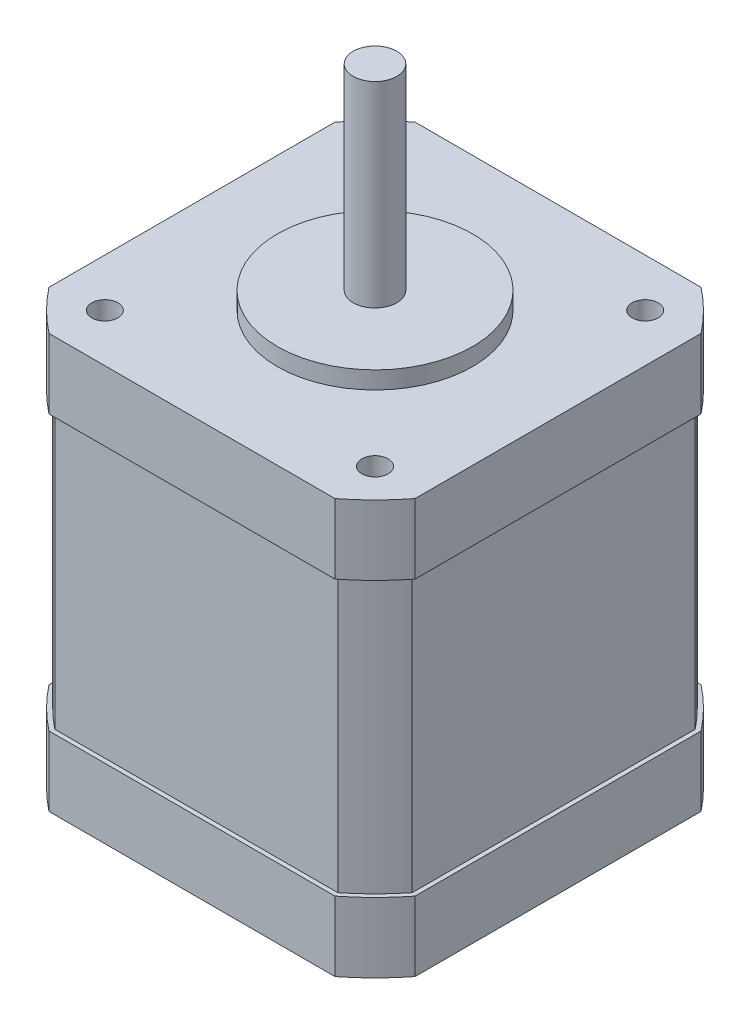
SolidWorks part; units mm, degrees
ref_plane "Front Plane" through (0, 0, 0) normal (0, 0, 1) x (1, 0, 0)
ref_plane "Top Plane" through (0, 0, 0) normal (0, 1, 0) x (1, 0, 0)
ref_plane "Right Plane" through (0, 0, 0) normal (1, 0, 0) x (0, 0, -1)
sketch "Sketch1" plane through (0, 0, 0) normal (0, 1, 0) x (1, 0, 0)
  line L1 (-16.408, 21) -> (16.408, 21)
  line L2 (-21, 16.408) -> (-21, -16.408)
  line L3 (-16.408, -21) -> (16.408, -21)
  line L4 (21, 16.408) -> (21, -16.408)
  line L5 (0, -21) -> (0, 21) construction
  line L6 (-21, 0) -> (21, 0) construction
  arc A0 (-16.408, 21) -> (-21, 16.408) centre (0, 0) ccw
  arc A1 (-21, -16.408) -> (-16.408, -21) centre (0, 0) ccw
  arc A2 (16.408, -21) -> (21, -16.408) centre (0, 0) ccw
  arc A3 (21, 16.408) -> (16.408, 21) centre (0, 0) ccw
  dimension "D1" = 53.3
  dimension "D2" = 42
extrude "Boss-Extrude1" add sketch "Sketch1" along normal blind 47.5
sketch "Sketch2" plane through (0, 47.5, 0) normal (0, 1, 0) x (1, 0, 0)
  line L1 (-15.4998, -15.4998) -> (15.4998, -15.4998) construction
  line L2 (-15.4998, -15.4998) -> (-15.4998, 15.4998) construction
  line L3 (-15.4998, 15.4998) -> (15.4998, 15.4998) construction
  line L4 (15.4998, -15.4998) -> (15.4998, 15.4998) construction
  line L5 (0, 15.4998) -> (0, -15.4998) construction
  line L6 (-15.4998, 0) -> (15.4998, 0) construction
  circle A1 centre (-15.4998, 15.4998) radius 1.5
  circle A2 centre (-15.4998, -15.4998) radius 1.5
  circle A3 centre (15.4998, -15.4998) radius 1.5
  circle A4 centre (15.4998, 15.4998) radius 1.5
  point P0 (0, 0)
  dimension "D2" = 3
  dimension "D1" = 43.84
extrude "Cut-Extrude1" cut sketch "Sketch2" against normal blind 8
sketch "Sketch3" plane through (0, 47.5, 0) normal (0, 1, 0) x (1, 0, 0)
  circle A0 centre (0, 0) radius 11.2
  dimension "D1" = 22.4
extrude "Boss-Extrude2" add sketch "Sketch3" along normal blind 2
sketch "Sketch4" plane through (0, 49.5, 0) normal (0, 1, 0) x (1, 0, 0)
  circle A0 centre (0, 0) radius 2.5
  dimension "D1" = 5
extrude "Boss-Extrude3" add sketch "Sketch4" along normal blind 22.5
sketch "Sketch5" plane through (0, 47.5, 0) normal (0, 1, 0) x (1, 0, 0)
  line L8 (-20.5, 16.2349) -> (-20.5, -16.2349)
  line L9 (-16.2349, -20.5) -> (16.2349, -20.5)
  line L10 (20.5, -16.2349) -> (20.5, 16.2349)
  line L11 (16.2349, 20.5) -> (-16.2349, 20.5)
  line L12 (-20.5, 16.2349) -> (-20.5, -16.2349)
  line L13 (-16.2349, -20.5) -> (16.2349, -20.5)
  line L14 (20.5, -16.2349) -> (20.5, 16.2349)
  line L15 (16.2349, 20.5) -> (-16.2349, 20.5)
  arc A8 (-16.2349, 20.5) -> (-20.5, 16.2349) centre (0, 0) ccw
  arc A9 (-20.5, -16.2349) -> (-16.2349, -20.5) centre (0, 0) ccw
  arc A10 (16.2349, -20.5) -> (20.5, -16.2349) centre (0, 0) ccw
  arc A11 (20.5, 16.2349) -> (16.2349, 20.5) centre (0, 0) ccw
  arc A12 (-16.2349, 20.5) -> (-20.5, 16.2349) centre (0, 0) ccw
  arc A13 (-20.5, -16.2349) -> (-16.2349, -20.5) centre (0, 0) ccw
  arc A14 (16.2349, -20.5) -> (20.5, -16.2349) centre (0, 0) ccw
  arc A15 (20.5, 16.2349) -> (16.2349, 20.5) centre (0, 0) ccw
  dimension "D1" = 0.5
extrude "Cut-Extrude2" cut sketch "Sketch5" against normal offset from surface (31.5 mm away) 8 from offset 8 flip side to cut up to face at (0, 0, 0)
